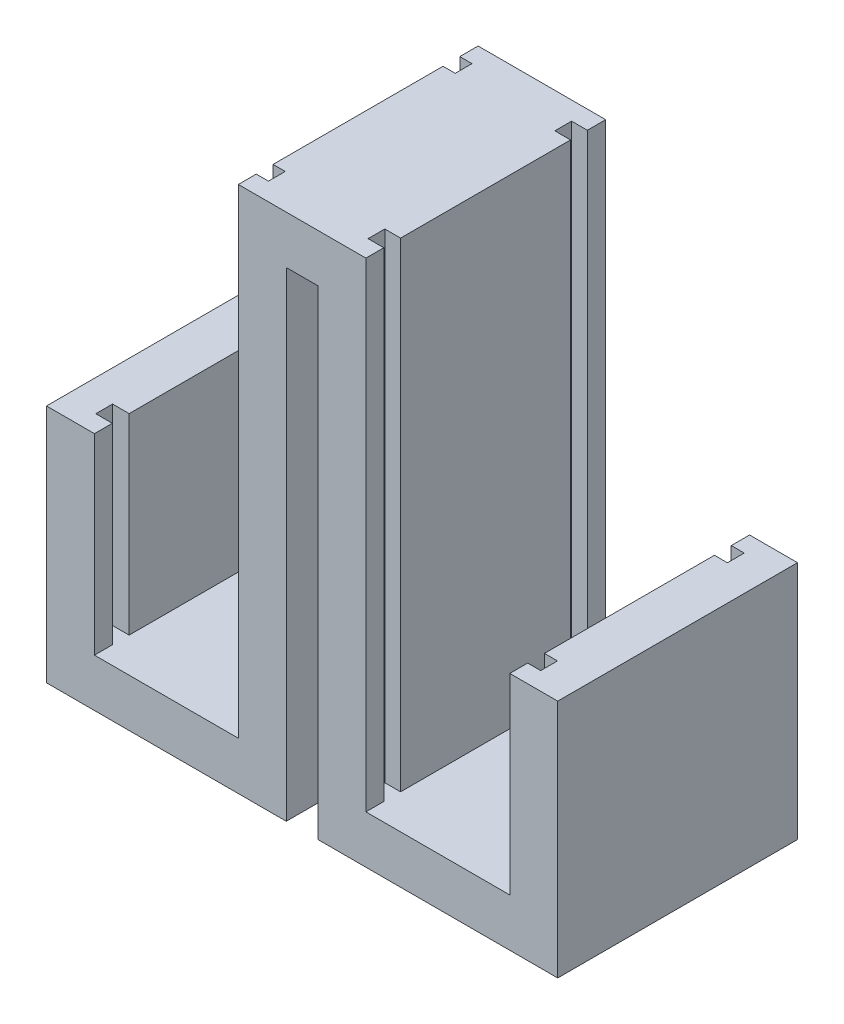
SolidWorks part; units mm, degrees
ref_plane "Plan de face" through (0, 0, 0) normal (0, 0, 1) x (1, 0, 0)
ref_plane "Plan de dessus" through (0, 0, 0) normal (0, 1, 0) x (1, 0, 0)
ref_plane "Plan de droite" through (0, 0, 0) normal (1, 0, 0) x (0, 0, -1)
sketch "Esquisse1" plane through (0, 0, 0) normal (0, 0, 1) x (1, 0, 0)
  line L0 (0, 0) -> (0, 100)
  line L1 (0, 100) -> (6.6, 100)
  line L2 (6.6, 100) -> (6.6, 0)
  line L3 (6.6, 0) -> (56.6, 0)
  line L4 (56.6, 0) -> (56.6, 50)
  line L5 (0, 0) -> (-50, 0)
  line L6 (-50, 0) -> (-50, 50)
  dimension "D1" = 6.6
  dimension "D2" = 100
  dimension "D3" = 50
  dimension "D4" = 50
  dimension "D5" = 50
  dimension "D6" = 50
extrude "Extru.-Mince1" add sketch "Esquisse1" along normal blind 50 thin thin type one direction wall 10
sketch "Esquisse2" plane through (0, 10, 0) normal (0, 1, 0) x (1, 0, 0)
  line L1 (-43.455, -3.8211) -> (-7.455, -3.8211)
  line L2 (-43.455, -3.8211) -> (-43.455, -7.3211)
  line L3 (-43.455, -7.3211) -> (-7.455, -7.3211)
  line L4 (-7.455, -3.8211) -> (-7.455, -7.3211)
  line L5 (-43.455, -42.7653) -> (-7.455, -42.7653)
  line L6 (-43.455, -42.7653) -> (-43.455, -46.2653)
  line L7 (-43.455, -46.2653) -> (-7.455, -46.2653)
  line L8 (-7.455, -42.7653) -> (-7.455, -46.2653)
  line L9 (13.3126, -3.8211) -> (49.3126, -3.8211)
  line L10 (13.3126, -3.8211) -> (13.3126, -7.3211)
  line L11 (13.3126, -7.3211) -> (49.3126, -7.3211)
  line L12 (49.3126, -3.8211) -> (49.3126, -7.3211)
  line L13 (13.3126, -42.7653) -> (49.3126, -42.7653)
  line L14 (13.3126, -42.7653) -> (13.3126, -46.2653)
  line L15 (13.3126, -46.2653) -> (49.3126, -46.2653)
  line L16 (49.3126, -42.7653) -> (49.3126, -46.2653)
  dimension "D1" = 3.5
  dimension "D2" = 36
  dimension "D3" = 3.5
  dimension "D4" = 36
  dimension "D5" = 36
extrude "Enlèv. mat.-Extru.1" cut sketch "Esquisse2" along normal up to surface (100 mm away) up to face at (3.3, 110, 25)
